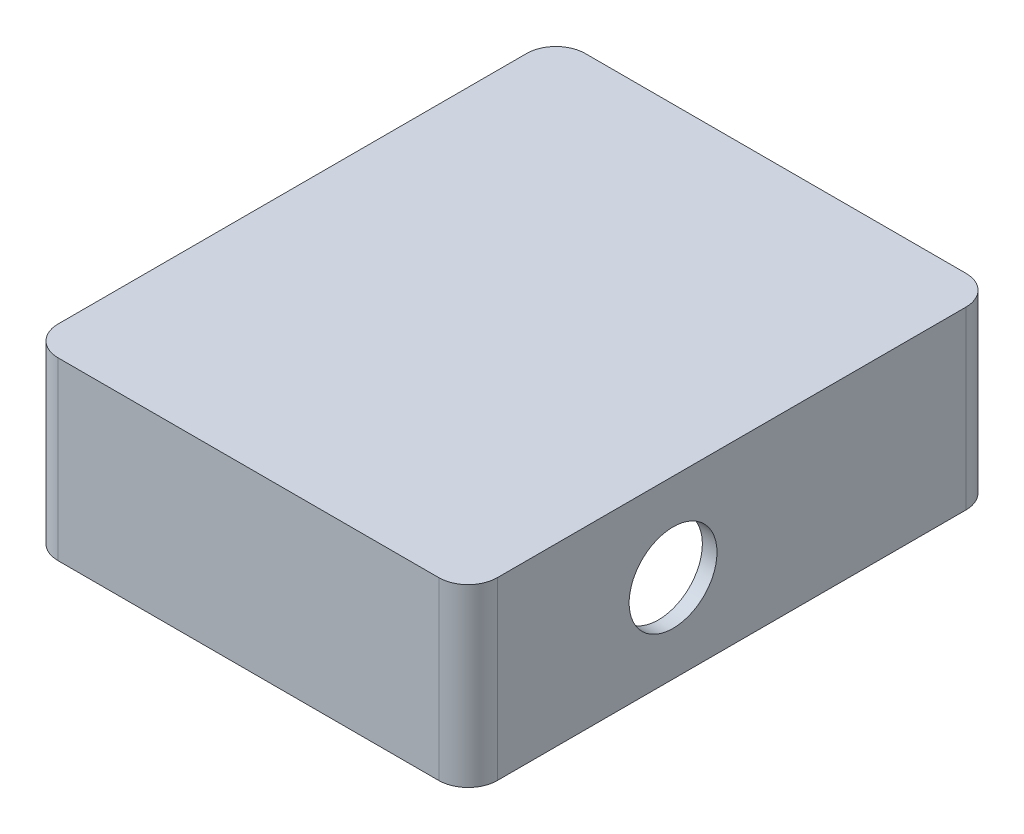
SolidWorks part; units mm, degrees
ref_plane "Front Plane" through (0, 0, 0) normal (0, 0, 1) x (1, 0, 0)
ref_plane "Top Plane" through (0, 0, 0) normal (0, 1, 0) x (1, 0, 0)
ref_plane "Right Plane" through (0, 0, 0) normal (1, 0, 0) x (0, 0, -1)
sketch "Sketch1" plane through (0, 0, 0) normal (0, 1, 0) x (1, 0, 0)
  line L1 (5, 0) -> (70, 0)
  line L2 (0, 5) -> (0, 85)
  line L3 (5, 90) -> (70, 90)
  line L4 (75, 5) -> (75, 85)
  arc A0 (5, 0) -> (0, 5) centre (5, 5) cw
  arc A1 (70, 0) -> (75, 5) centre (70, 5) ccw
  arc A2 (70, 90) -> (75, 85) centre (70, 85) cw
  arc A3 (0, 85) -> (5, 90) centre (5, 85) cw
  point P7 (0, 0)
  point P10 (75, 0)
  point P15 (0, 90)
  point P21 (35, 75)
  dimension "D3" = 5
  dimension "D1" = 90
  dimension "D2" = 75
extrude "Boss-Extrude1" add sketch "Sketch1" along normal blind 30 contours L2 A3 L3 A2 L4 A1 L1 A0
sketch "Sketch3" plane through (0, 0, 0) normal (0, -1, 0) x (-1, 0, 0)
  line L0 (0, 0) -> (0, 2.5) construction
  line L1 (0, 2.5) -> (-2.5, 2.5) construction
  line L3 (-7.5, 2.5) -> (-67.5, 2.5)
  line L4 (-2.5, 7.5) -> (-2.5, 82.5)
  line L5 (-7.5, 87.5) -> (-67.5, 87.5)
  line L6 (-72.5, 7.5) -> (-72.5, 82.5)
  line L7 (-75, 5) -> (-75, 85) construction
  line L8 (-5, 90) -> (-70, 90) construction
  arc A0 (-2.5, 7.5) -> (-7.5, 2.5) centre (-7.5, 7.5) cw
  arc A1 (-67.5, 2.5) -> (-72.5, 7.5) centre (-67.5, 7.5) cw
  arc A2 (-67.5, 87.5) -> (-72.5, 82.5) centre (-67.5, 82.5) ccw
  arc A3 (-2.5, 82.5) -> (-7.5, 87.5) centre (-7.5, 82.5) ccw
  point P16 (-72.5, 2.5)
  point P19 (-72.5, 87.5)
  dimension "D5" = 5
  dimension "D1" = 2.5
  dimension "D2" = 2.5
  dimension "D3" = 2.5
  dimension "D4" = 2.5
extrude "Cut-Extrude3" cut sketch "Sketch3" against normal blind 28
sketch "Sketch5" plane through (75, 0, 0) normal (1, 0, 0) x (0, 0, -1)
  line L0 (90, 30) -> (90, 0) construction
  line L1 (5, 30) -> (85, 30) construction
  line L2 (0, 30) -> (0, 0) construction
  circle A0 centre (35, 15) radius 7.5
  point P6 (0, 0)
  dimension "D1" = 15
  dimension "D3" = 15
  dimension "D2" = 55
extrude "Cut-Extrude5" cut sketch "Sketch5" against normal blind 4
